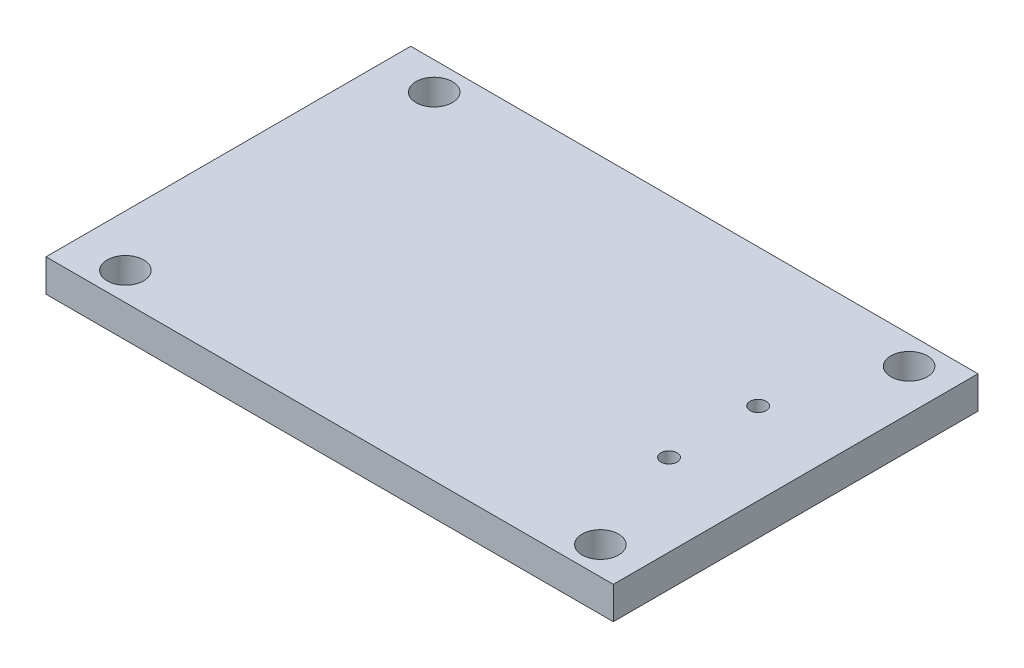
SolidWorks part; units mm, degrees
material "E-Glass Fiber"
ref_plane "Front Plane" through (0, 0, 0) normal (0, 0, 1) x (1, 0, 0)
ref_plane "Top Plane" through (0, 0, 0) normal (0, 1, 0) x (1, 0, 0)
ref_plane "Right Plane" through (0, 0, 0) normal (1, 0, 0) x (0, 0, -1)
sketch "Sketch1" plane through (0, 0, 0) normal (0, 1, 0) x (1, 0, 0)
  line L0 (0, 7.62) -> (3.78, 7.62) construction
  line L1 (3.78, 16.62) -> (31.78, 16.62)
  line L2 (3.78, 16.62) -> (3.78, -1.38)
  line L3 (3.78, -1.38) -> (31.78, -1.38)
  line L4 (31.78, 16.62) -> (31.78, -1.38)
  line L5 (0, 0) -> (35.56, 0) construction
  line L6 (0, 0) -> (0, 15.24) construction
  line L7 (0, 15.24) -> (35.56, 15.24) construction
  line L8 (35.56, 0) -> (35.56, 15.24) construction
  line L10 (35.56, 7.62) -> (31.78, 7.62) construction
  dimension "D1" = 28
  dimension "D2" = 18
  dimension "D3" = 15.24
  dimension "D4" = 35.56
extrude "Boss-Extrude2" add sketch "Sketch1" along normal blind 1.6
sketch "Sketch4" plane through (0, 0, 0) normal (0, 1, 0) x (1, 0, 0)
  line L0 (-0.88, 0) -> (0.88, 0) construction
  line L2 (3.78, 16.62) -> (3.78, -1.38) construction
  circle A0 centre (29.76, 15.24) radius 0.9
  circle A1 centre (29.76, 0) radius 0.9
  circle A2 centre (6.32, 0) radius 0.9
  circle A3 centre (6.32, 15.24) radius 0.9
  dimension "D3" = 1.8
  dimension "D1" = 23.44
  dimension "D2" = 2.54
  dimension "D4" = 15.24
  dimension "D5" = 15.24
extrude "Cut-Extrude5" cut sketch "Sketch4" along normal blind 1.6
sketch "Sketch5" plane through (0, 1.6, 0) normal (0, 1, 0) x (1, 0, 0)
  circle A0 centre (29.76, 15.24) radius 0.9
  circle A1 centre (29.76, 15.24) radius 1.275
  circle A2 centre (29.76, 15.24) radius 0.9 construction
  circle A3 centre (29.76, 0) radius 0.9
  circle A4 centre (29.76, 0) radius 0.9 construction
  circle A5 centre (29.76, 0) radius 1.275
  circle A6 centre (6.32, 15.24) radius 0.9
  circle A7 centre (6.32, 15.24) radius 1.275
  circle A8 centre (6.32, 0) radius 0.9
  circle A9 centre (6.32, 0) radius 1.275
  circle A10 centre (6.32, 15.24) radius 0.9 construction
  circle A11 centre (6.32, 0) radius 0.9 construction
  dimension "D1" = 2.55
extrude "Boss-Extrude3" [suppressed] add sketch "Sketch5" along normal blind 0.1
sketch "Sketch6" plane through (0, 0, 0) normal (1, 0, 0) x (0, 0, -1)
  line L0 (0, 1.6) -> (0.9, 1.6)
  line L1 (-1.38, 1.6) -> (16.62, 1.6) construction
  line L2 (0.2252, 3.1) -> (0, 3.1)
  line L3 (0, 0.88) -> (0, -0.88) construction
  line L4 (0, 3.1) -> (0, 1.6)
  line L5 (0, 1.3722) -> (0, 3.4408) construction
  arc A0 (0.9, 1.6) -> (0.7139, 2.2122) centre (-0.2, 1.6) ccw
  arc A1 (0.7139, 2.2122) -> (0.4221, 2.9352) centre (2.2924, 3.2697) cw
  arc A2 (0.4221, 2.9352) -> (0.2252, 3.1) centre (0.2252, 2.9) ccw
  point P16 (0.4, 3.1)
  dimension "D4" = 1.1
  dimension "D5" = 1.9
  dimension "D6" = 0.2
  dimension "D1" = 1.5
  dimension "D2" = 0.8
  dimension "D3" = 1.8
revolve "Revolve1" [suppressed] add sketch "Sketch6" angle 360 about L5
pattern_linear "LPattern2" [suppressed] count 2 spacing 15.24 count 15 spacing 2.54
ref_plane "Plane3" through (0, 0, -5.08) normal (0, 0, 1) x (1, 0, 0)
sketch "Sketch7" plane through (0, 0, -5.08) normal (0, 0, 1) x (1, 0, 0)
  line L0 (0.127, 3.889) -> (0.127, -2.5597) construction
  line L2 (0, -1.705) -> (0, 1.705) construction
  line L3 (0.127, 0) -> (1.027, 0)
  line L4 (9.9, 0) -> (-9.9, 0) construction
  line L5 (0.127, 0) -> (0.127, -1.5)
  line L6 (0.127, -1.5) -> (0.3395, -1.5)
  arc A0 (0.538, -1.325) -> (0.807, -0.66) centre (1.927, -1.5) cw
  arc A1 (0.807, -0.66) -> (1.027, 0) centre (-0.073, 0) ccw
  arc A2 (0.3395, -1.5) -> (0.538, -1.325) centre (0.3395, -1.3) ccw
  point P16 (0.527, -1.5)
  dimension "D5" = 1.1
  dimension "D6" = 0.2
  dimension "D1" = 0.127
  dimension "D2" = 1.5
  dimension "D3" = 0.8
  dimension "D4" = 1.8
revolve "Revolve2" [suppressed] add sketch "Sketch7" angle 360 about L0
pattern_linear "LPattern3" [suppressed] count 2 spacing 2.54 count 3 spacing 2.54
sketch "Sketch8" plane through (0, 0, 0) normal (0, -1, 0) x (1, 0, 0)
  circle A0 centre (29.76, 0) radius 0.9
  circle A1 centre (29.76, 0) radius 1.275
  circle A2 centre (29.76, -15.24) radius 1.275
  circle A3 centre (29.76, -15.24) radius 0.9
  circle A4 centre (29.76, -15.24) radius 0.9 construction
  circle A5 centre (29.76, 0) radius 0.9 construction
  circle A6 centre (6.32, 0) radius 0.9
  circle A7 centre (6.32, 0) radius 1.275
  circle A8 centre (6.32, -15.24) radius 0.9
  circle A9 centre (6.32, -15.24) radius 1.275
  circle A10 centre (6.32, 0) radius 0.9 construction
  circle A11 centre (6.32, -15.24) radius 0.9 construction
  dimension "D1" = 2.55
extrude "Boss-Extrude4" [suppressed] add sketch "Sketch8" along normal blind 0.1
sketch "Sketch9" plane through (0, 0, 0) normal (0, 1, 0) x (1, 0, 0)
  line L0 (-0.88, 0) -> (0.88, 0) construction
  line L1 (31.78, -1.38) -> (31.78, 16.62) construction
  circle A0 centre (27.73, 5.42) radius 0.4
  circle A1 centre (27.73, 9.82) radius 0.4
  dimension "D1" = 0.8
  dimension "D2" = 4.4
  dimension "D3" = 5.42
  dimension "D4" = 4.05
extrude "Cut-Extrude6" cut sketch "Sketch9" along normal blind 10
